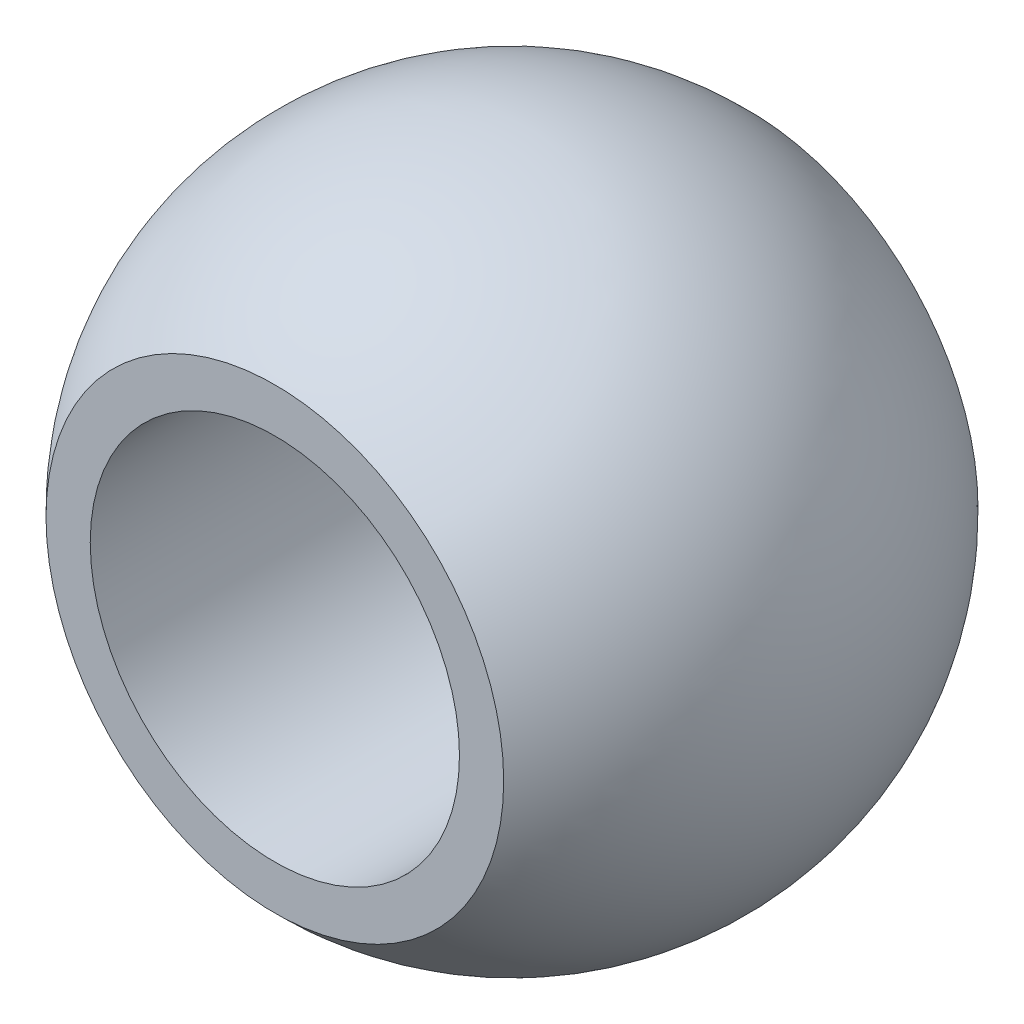
SolidWorks part; units mm, degrees
material "AISI 4130 Steel, normalized at 870C"
ref_plane "Front Plane" through (0, 0, 0) normal (0, 0, 1) x (1, 0, 0)
ref_plane "Top Plane" through (0, 0, 0) normal (0, 1, 0) x (1, 0, 0)
ref_plane "Right Plane" through (0, 0, 0) normal (1, 0, 0) x (0, 0, -1)
sketch "Sketch1" plane through (0, 0, 0) normal (0, 0, 1) x (1, 0, 0)
  circle A0 centre (0, 0) radius 9.5
  dimension "D1" = 19
sketch "Sketch2" plane through (0, 0, 0) normal (0, 0, 1) x (1, 0, 0)
  line L0 (0, 9.9187) -> (0, -9.9187)
  line L1 (0, 12.923) -> (0, -12.923) construction
  arc A0 (0, -9.9187) -> (0, 9.9187) centre (0, 0) ccw
  dimension "D1" = 9.9187
sketch "Sketch3" plane through (0, 0, 0) normal (0, 1, 0) x (1, 0, 0)
  line L1 (-19.9993, 7.1374) -> (19.9993, 7.1374)
  line L2 (-19.9993, 7.1374) -> (-19.9993, -7.1374)
  line L3 (-19.9993, -7.1374) -> (19.9993, -7.1374)
  line L4 (19.9993, 7.1374) -> (19.9993, -7.1374)
  line L5 (-19.9993, 7.1374) -> (19.9993, -7.1374) construction
  line L6 (-19.9993, -7.1374) -> (19.9993, 7.1374) construction
  point P0 (0, 0)
  dimension "D1" = 7.1374
sketch "Sketch4" plane through (0, 0, 0) normal (0, 0, 1) x (1, 0, 0)
  circle A0 centre (0, 0) radius 5.5563
  dimension "D1" = 11.1125
revolve "Revolve2" add sketch "Sketch2" angle 360 about L1
extrude "Cut-Extrude3" cut sketch "Sketch4" against normal through all and the other way through all
extrude "Cut-Extrude4" cut sketch "Sketch3" against normal through all and the other way through all flip side to cut
